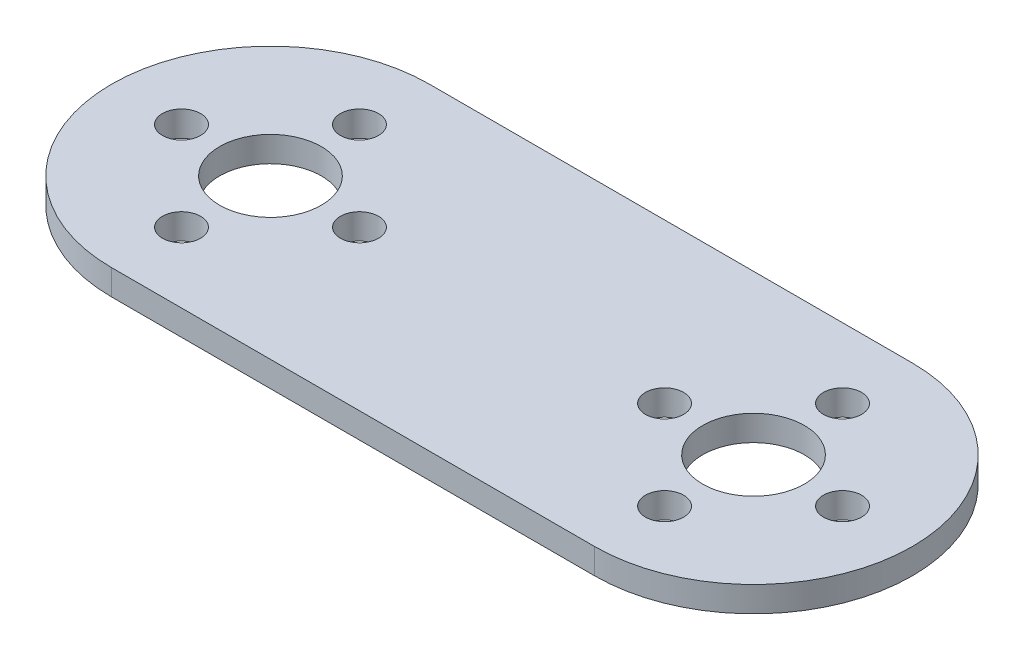
SolidWorks part; units mm, degrees
ref_plane "Front Plane" through (0, 0, 0) normal (0, 0, 1) x (1, 0, 0)
ref_plane "Top Plane" through (0, 0, 0) normal (0, 1, 0) x (1, 0, 0)
ref_plane "Right Plane" through (0, 0, 0) normal (1, 0, 0) x (0, 0, -1)
sketch "Sketch1" plane through (0, 0, 0) normal (0, 1, 0) x (1, 0, 0)
  line L1 (19, -12.5) -> (-19, -12.5)
  line L3 (19, 12.5) -> (-19, 12.5)
  line L5 (19, -12.5) -> (-19, 12.5) construction
  line L6 (19, 12.5) -> (-19, -12.5) construction
  arc A0 (19, 12.5) -> (19, -12.5) centre (19, 0) cw
  arc A1 (-19, 12.5) -> (-19, -12.5) centre (-19, 0) ccw
  circle A2 centre (-19, 0) radius 4
  circle A4 centre (19, 0) radius 4
  circle A6 centre (-19, 7) radius 1.5
  circle A7 centre (-12, 0) radius 1.5
  circle A8 centre (-26, 0) radius 1.5
  circle A9 centre (-19, -7) radius 1.5
  circle A10 centre (12, 0) radius 1.5
  circle A11 centre (19, 7) radius 1.5
  circle A12 centre (26, 0) radius 1.5
  circle A13 centre (19, -7) radius 1.5
  point P0 (0, 0)
  dimension "D3" = 3
  dimension "D4" = 3
  dimension "D5" = 3
  dimension "D6" = 3
  dimension "D7" = 3
  dimension "D8" = 3
  dimension "D9" = 3
  dimension "D10" = 3
  dimension "D13" = 8
  dimension "D14" = 8
  dimension "D1" = 38
  dimension "D2" = 25
extrude "Boss-Extrude1" add sketch "Sketch1" along normal blind 2
